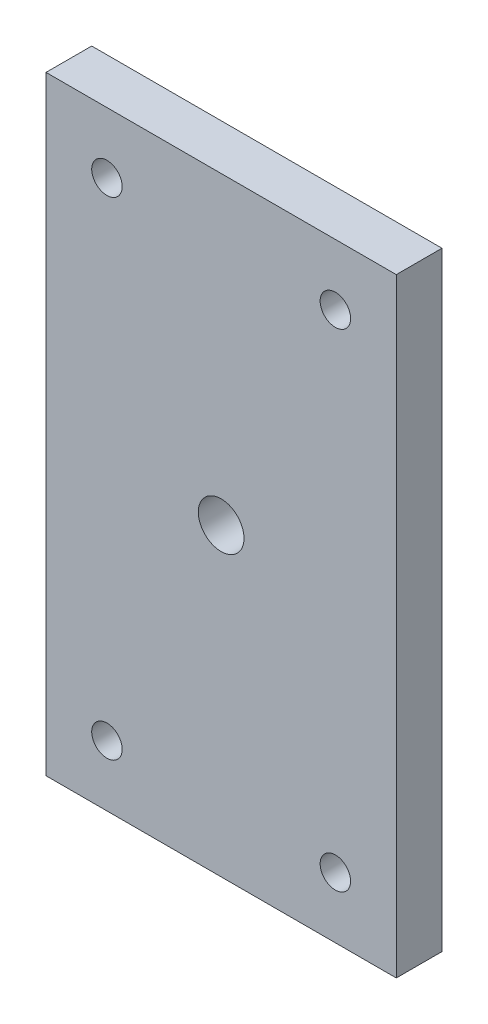
SolidWorks part; units mm, degrees
ref_plane "Plan de face" through (0, 0, 0) normal (0, 0, 1) x (1, 0, 0)
ref_plane "Plan de dessus" through (0, 0, 0) normal (0, 1, 0) x (1, 0, 0)
ref_plane "Plan de droite" through (0, 0, 0) normal (1, 0, 0) x (0, 0, -1)
sketch "Sketch1" plane through (0, 0, 0) normal (0, 0, 1) x (1, 0, 0)
  line L1 (0, 0) -> (23, 0)
  line L2 (0, 0) -> (0, 40)
  line L3 (0, 40) -> (23, 40)
  line L4 (23, 0) -> (23, 40)
  dimension "D1" = 23
  dimension "D2" = 40
extrude "Boss-Extrude1" add sketch "Sketch1" along normal blind 3
sketch "Sketch2" plane through (0, 0, 3) normal (0, 0, 1) x (1, 0, 0)
  line L0 (23, 0) -> (0, 40) construction
  circle A0 centre (11.5, 20) radius 1.5
  dimension "D1" = 3
extrude "Cut-Extrude1" cut sketch "Sketch2" against normal through all
ref_plane "Plane1" through (11.5, 0, 0) normal (1, 0, 0) x (0, 0, -1)
sketch "Sketch3" plane through (11.5, 0, 0) normal (1, 0, 0) x (0, 0, -1)
  line L0 (0, 20) -> (-3, 20) construction
  line L1 (0, 0) -> (0, 40) construction
  line L2 (-3, 0) -> (-3, 40) construction
  line L3 (0, 40) -> (0, 0) construction
  line L4 (-0.7529, 1) -> (0, 1) construction
  line L5 (0, 13.697) -> (0, 12.303)
  line L6 (0, 11.697) -> (0, 10.303)
  line L7 (0, 9.697) -> (0, 8.303)
  line L8 (0, 7.697) -> (0, 6.303)
  line L9 (0, 5.697) -> (0, 4.303)
  line L10 (0, 3.697) -> (0, 2.303)
  line L11 (0, 1.697) -> (0, 0.303)
  arc A0 (0, 0.303) -> (-0.105, 0.4461) centre (-0.15, 0.303) ccw
  arc A1 (-0.105, 0.4461) -> (-0.2432, 0.5011) centre (0.195, 1.4) cw
  arc A2 (-0.2432, 0.5011) -> (-0.2432, 1.4989) centre (0, 1) cw
  arc A3 (-0.105, 1.5539) -> (-0.2432, 1.4989) centre (0.195, 0.6) ccw
  arc A4 (0, 1.697) -> (-0.105, 1.5539) centre (-0.15, 1.697) cw
  arc A5 (0, 2.303) -> (-0.105, 2.4461) centre (-0.15, 2.303) ccw
  arc A6 (-0.105, 2.4461) -> (-0.2432, 2.5011) centre (0.195, 3.4) cw
  arc A7 (-0.2432, 2.5011) -> (-0.2432, 3.4989) centre (0, 3) cw
  arc A8 (-0.105, 3.5539) -> (-0.2432, 3.4989) centre (0.195, 2.6) ccw
  arc A9 (0, 3.697) -> (-0.105, 3.5539) centre (-0.15, 3.697) cw
  arc A10 (0, 4.303) -> (-0.105, 4.4461) centre (-0.15, 4.303) ccw
  arc A11 (-0.105, 4.4461) -> (-0.2432, 4.5011) centre (0.195, 5.4) cw
  arc A12 (-0.2432, 4.5011) -> (-0.2432, 5.4989) centre (0, 5) cw
  arc A13 (-0.105, 5.5539) -> (-0.2432, 5.4989) centre (0.195, 4.6) ccw
  arc A14 (0, 5.697) -> (-0.105, 5.5539) centre (-0.15, 5.697) cw
  arc A15 (0, 6.303) -> (-0.105, 6.4461) centre (-0.15, 6.303) ccw
  arc A16 (-0.105, 6.4461) -> (-0.2432, 6.5011) centre (0.195, 7.4) cw
  arc A17 (-0.2432, 6.5011) -> (-0.2432, 7.4989) centre (0, 7) cw
  arc A18 (-0.105, 7.5539) -> (-0.2432, 7.4989) centre (0.195, 6.6) ccw
  arc A19 (0, 7.697) -> (-0.105, 7.5539) centre (-0.15, 7.697) cw
  arc A20 (0, 8.303) -> (-0.105, 8.4461) centre (-0.15, 8.303) ccw
  arc A21 (-0.105, 8.4461) -> (-0.2432, 8.5011) centre (0.195, 9.4) cw
  arc A22 (-0.2432, 8.5011) -> (-0.2432, 9.4989) centre (0, 9) cw
  arc A23 (-0.105, 9.5539) -> (-0.2432, 9.4989) centre (0.195, 8.6) ccw
  arc A24 (0, 9.697) -> (-0.105, 9.5539) centre (-0.15, 9.697) cw
  arc A25 (0, 10.303) -> (-0.105, 10.4461) centre (-0.15, 10.303) ccw
  arc A26 (-0.105, 10.4461) -> (-0.2432, 10.5011) centre (0.195, 11.4) cw
  arc A27 (-0.2432, 10.5011) -> (-0.2432, 11.4989) centre (0, 11) cw
  arc A28 (-0.105, 11.5539) -> (-0.2432, 11.4989) centre (0.195, 10.6) ccw
  arc A29 (0, 11.697) -> (-0.105, 11.5539) centre (-0.15, 11.697) cw
  arc A30 (0, 12.303) -> (-0.105, 12.4461) centre (-0.15, 12.303) ccw
  arc A31 (-0.105, 12.4461) -> (-0.2432, 12.5011) centre (0.195, 13.4) cw
  arc A32 (-0.2432, 12.5011) -> (-0.2432, 13.4989) centre (0, 13) cw
  arc A33 (-0.105, 13.5539) -> (-0.2432, 13.4989) centre (0.195, 12.6) ccw
  arc A34 (0, 13.697) -> (-0.105, 13.5539) centre (-0.15, 13.697) cw
  dimension "D1" = 0.15
  dimension "D2" = 1
  dimension "D3" = 0.555
  dimension "D4" = 0.4
  dimension "D6" = 7
extrude "Cut-Extrude4" cut sketch "Sketch3" against normal blind 5 and the other way blind 5
ref_plane "Plane2" through (0, 20, 0) normal (0, -1, 0) x (-1, 0, 0)
mirror "Mirror1" about plane through (0, 20, 0) normal (0, -1, 0) of "Cut-Extrude4"
sketch "Sketch4" plane through (0, 0, 0) normal (0, 0, -1) x (-1, 0, 0)
  line L0 (-11.5, 40) -> (-11.5, 0) construction
  line L1 (-23, 40) -> (0, 40) construction
  line L2 (0, 0) -> (-23, 0) construction
  line L3 (-23, 0) -> (-23, 40) construction
  circle A0 centre (-19, 36) radius 1
  circle A1 centre (-19, 4) radius 1
  circle A2 centre (-4, 4) radius 1
  circle A3 centre (-4, 36) radius 1
  dimension "D1" = 2
  dimension "D2" = 2
  dimension "D3" = 4
  dimension "D4" = 4
  dimension "D5" = 4
  dimension "D6" = 4
extrude "Cut-Extrude5" cut sketch "Sketch4" against normal through all
